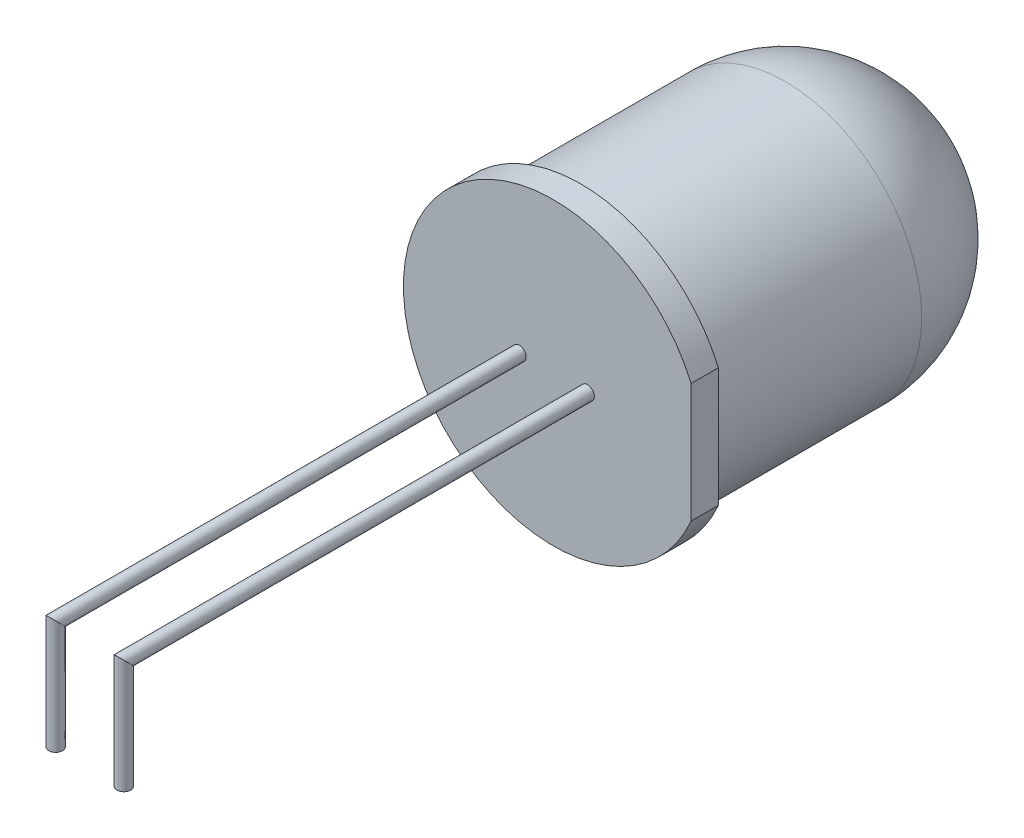
SolidWorks part; units mm, degrees
ref_plane "Face" through (0, 0, 0) normal (0, 0, 1) x (1, 0, 0)
ref_plane "Dessus" through (0, 0, 0) normal (0, 1, 0) x (1, 0, 0)
ref_plane "Droite" through (0, 0, 0) normal (1, 0, 0) x (0, 0, -1)
sketch "Esquisse1" plane through (0, 0, 0) normal (0, 0, 1) x (1, 0, 0)
  circle A0 centre (0, 0) radius 5
extrude "Base-Extrusion" add sketch "Esquisse1" along normal blind 13.5
sketch "Esquisse2" plane through (0, 0, 13.5) normal (0, 0, 1) x (1, 0, 0)
  line L0 (5.0476, -2.4917) -> (5.0476, 2.5621) construction
  line L1 (5.0476, 2.1843) -> (5.0476, -2.1843)
  arc A0 (5.0476, 2.1843) -> (5.0476, -2.1843) centre (0, 0) ccw
extrude "Boss.-Extru.1" add sketch "Esquisse2" against normal blind 1
fillet "Congé1" radius 5 1 edges at (5, 0, 0)
sketch "Esquisse3" plane through (0, 0, 13.5) normal (0, 0, 1) x (1, 0, 0)
  line L0 (6.6041, 0) -> (-9.0558, 0) construction
  line L1 (0, -6.5869) -> (0, 7.9113) construction
  line L2 (-1.27, 2.2189) -> (-1.27, -1.5916) construction
  circle A0 centre (-1.25, 0) radius 0.25
  dimension "D1" = 1.27
ref_plane "Plan1" through (-1.25, 0, 0) normal (1, 0, 0) x (0, 0, -1)
sketch "Esquisse4" plane through (-1.25, 0, 0) normal (1, 0, 0) x (0, 0, -1)
  line L0 (-13.5, 0) -> (-33.943, 0) construction
  line L2 (-13.5, 6.7858) -> (-13.5, -8.0266) construction
  line L3 (-30.5, 5.6624) -> (-30.5, -6.9656) construction
  line L4 (-13.5, -6.5869) -> (-13.5, 7.9113) construction
  line L5 (-33.943, -4) -> (-13.0406, -4) construction
  line L6 (-13.5, 0) -> (-30.5, 0)
  line L7 (-30.5, 0) -> (-30.5, -4)
  dimension "D1" = 17
  dimension "D2" = 4
sweep "Balayage1" add profiles "Esquisse3" path "Esquisse4"
ref_plane "Plan2" through (0, 0, 0) normal (1, 0, 0) x (0, 0, -1)
mirror "Symétrie1" about plane through (0, 0, 0) normal (1, 0, 0) of "Balayage1"
